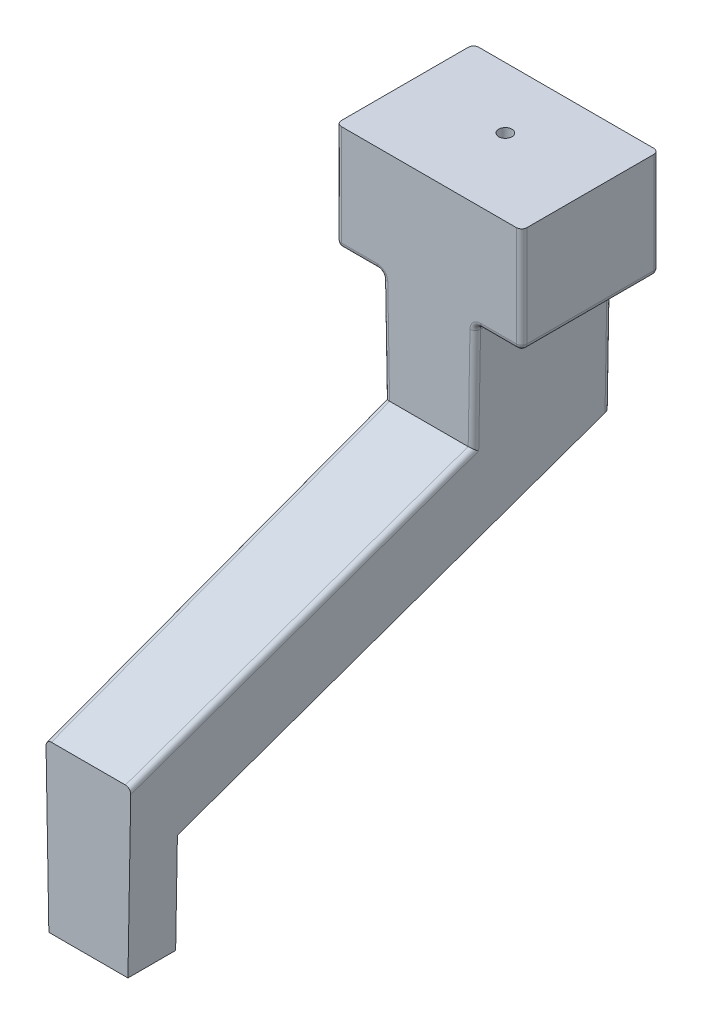
SolidWorks part; units mm, degrees
material "ABS"
ref_plane "Front Plane" through (0, 0, 0) normal (0, 0, 1) x (1, 0, 0)
ref_plane "Top Plane" through (0, 0, 0) normal (0, 1, 0) x (1, 0, 0)
ref_plane "Right Plane" through (0, 0, 0) normal (1, 0, 0) x (0, 0, -1)
sketch "Sketch1" plane through (0, 0, 0) normal (1, 0, 0) x (0, 0, -1)
  line L0 (-5.5621, 1.6696) -> (-5.5621, -0.2304)
  line L1 (-6.4621, 2.8992) -> (-0.0389, 5.2371)
  line L2 (-0.0389, 5.2371) -> (-0.0389, 9.2696)
  line L3 (-0.0389, 9.2696) -> (2.5536, 9.2696)
  line L6 (-6.4621, -0.2304) -> (-5.5621, -0.2304)
  line L7 (-6.4621, -0.2304) -> (-6.4621, 2.8992)
  line L8 (6.9061, -4.2681) -> (6.407, -3.9335) construction
  line L14 (-5.5621, 1.6696) -> (2.5536, 4.6234)
  line L15 (2.5536, 4.6234) -> (2.5536, 9.2696)
  line L17 (-6.4621, -0.2304) -> (-6.2771, -0.6271) construction
  line L20 (7.7076, -0.2304) -> (-6.3295, -0.2304) construction
  dimension "D1" = 9.5
  dimension "D2" = 110
  dimension "D3" = 1.9
  dimension "D4" = 0.9
sketch "Sketch4" plane through (0, 0, 0) normal (1, 0, 0) x (0, 0, -1)
  line L0 (5.9019, -1.4145) -> (5.9019, 2.1305) construction
  line L1 (-6.4621, -0.2304) -> (-6.4621, 2.8992) construction
  dimension "D1" = 12.364
extrude "Boss-Extrude1" add sketch "Sketch1" along normal blind 1.5 contours L2 L3 L15 L14 L0 L6 L7 L1
sketch "Sketch5" plane through (0, 0, 0) normal (-1, 0, 0) x (0, 0, 1)
  line L0 (0.0389, 5.2371) -> (0.0389, 9.2696) construction
  line L1 (-2.5536, 9.2696) -> (0.0389, 9.2696)
  line L2 (-2.5536, 9.2696) -> (-2.5536, 7.2696)
  line L3 (-2.5536, 7.2696) -> (0.0389, 7.2696)
  line L4 (0.0389, 9.2696) -> (0.0389, 7.2696)
  line L5 (-2.5536, 9.2696) -> (0.0389, 7.2696) construction
  line L6 (-2.5536, 7.2696) -> (0.0389, 9.2696) construction
  point P4 (-1.2573, 8.2696)
  dimension "D1" = 2
extrude "Boss-Extrude2" add sketch "Sketch5" along normal blind 1 and the other way blind 2.5
draft "Draft1" type of draft neutral plane draft angle 1 neutral plane "Top Plane" faces to draft 2 face at (1.5, 3.5634, 2.3774) face at (0, 3.5634, 2.3774) neutral plane through (0, 0, 0) neutral plane normal (0, 1, 0) reverse direction yes parameters "D1"=1
fillet "Fillet1" radius 0.1 18 edges at (1.6092, 6.2533, 0.0389) (-0.5634, 7.2696, -2.5536) (1.6269, 7.2696, -1.2573) (2.5, 7.2696, -1.2573) (2.5, 8.2696, -2.5536) (2.0634, 7.2696, -2.5536) (1.6038, 5.9465, -2.5536) (-0.1038, 5.9465, -2.5536) (-1, 8.2696, -2.5536) (-1, 7.2696, -1.2573) (-0.1269, 7.2696, -1.2573) (-0.1092, 6.2533, 0.0389) (-0.5634, 7.2696, 0.0389) (2.0634, 7.2696, 0.0389) (2.5, 8.2696, 0.0389) (-1, 8.2696, 0.0389) (1.571, 4.0681, 3.2505) (-0.071, 4.0681, 3.2505)
sketch "Sketch6" plane through (0, 9.2696, 0) normal (0, 1, 0) x (1, 0, 0)
  line L0 (0.75, 2.5536) -> (0.75, -0.5089) construction
  line L1 (2.4, 2.5536) -> (-0.9, 2.5536) construction
  circle A0 centre (0.75, 1.4036) radius 0.125
  dimension "D2" = 0.25
  dimension "D1" = 1.15
extrude "Cut-Extrude1" cut sketch "Sketch6" against normal blind 2.5
